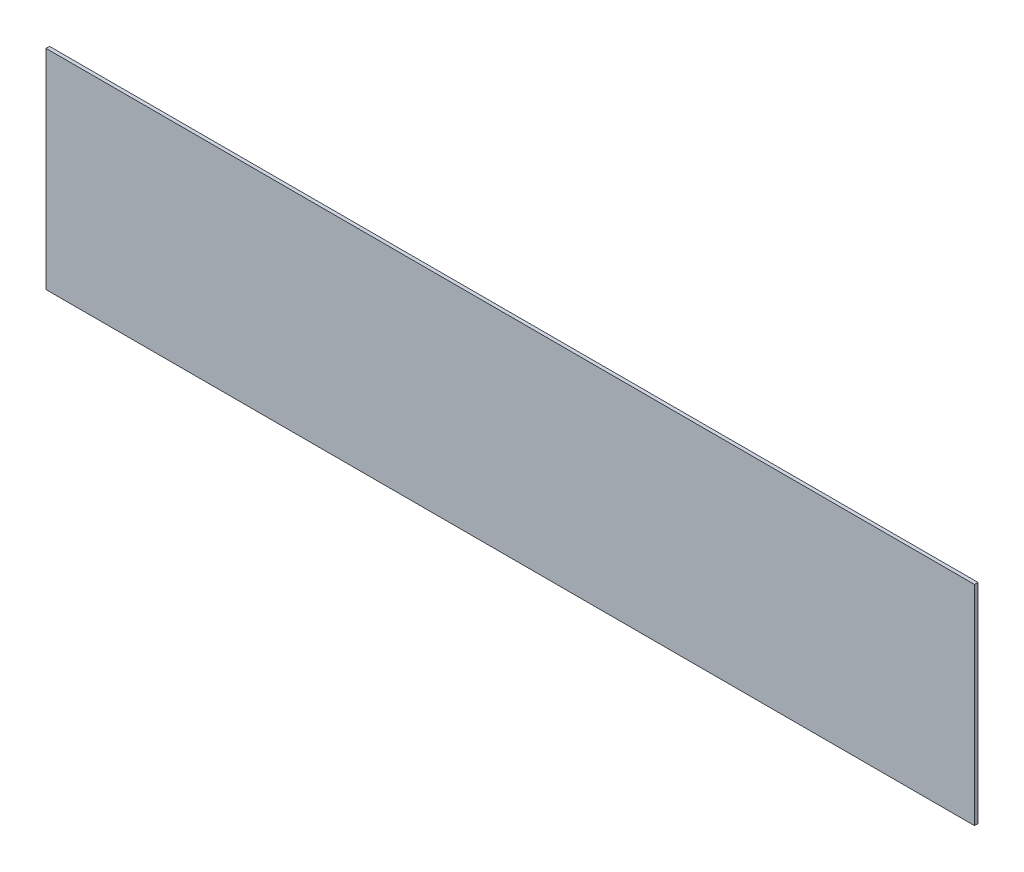
SolidWorks part; units mm, degrees
ref_plane "前基準面" through (0, 0, 0) normal (0, 0, 1) x (1, 0, 0)
ref_plane "上基準面" through (0, 0, 0) normal (0, 1, 0) x (1, 0, 0)
ref_plane "右基準面" through (0, 0, 0) normal (1, 0, 0) x (0, 0, -1)
sketch "草圖1" plane through (0, 0, 0) normal (0, 0, 1) x (1, 0, 0)
  line L1 (-269.0323, 14.7803) -> (130.9677, 14.7803)
  line L2 (-269.0323, 14.7803) -> (-269.0323, -75.2197)
  line L3 (-269.0323, -75.2197) -> (130.9677, -75.2197)
  line L4 (130.9677, 14.7803) -> (130.9677, -75.2197)
  dimension "D1" = 400
  dimension "D2" = 90
extrude "填料-伸長1" add sketch "草圖1" along normal blind 1.5
